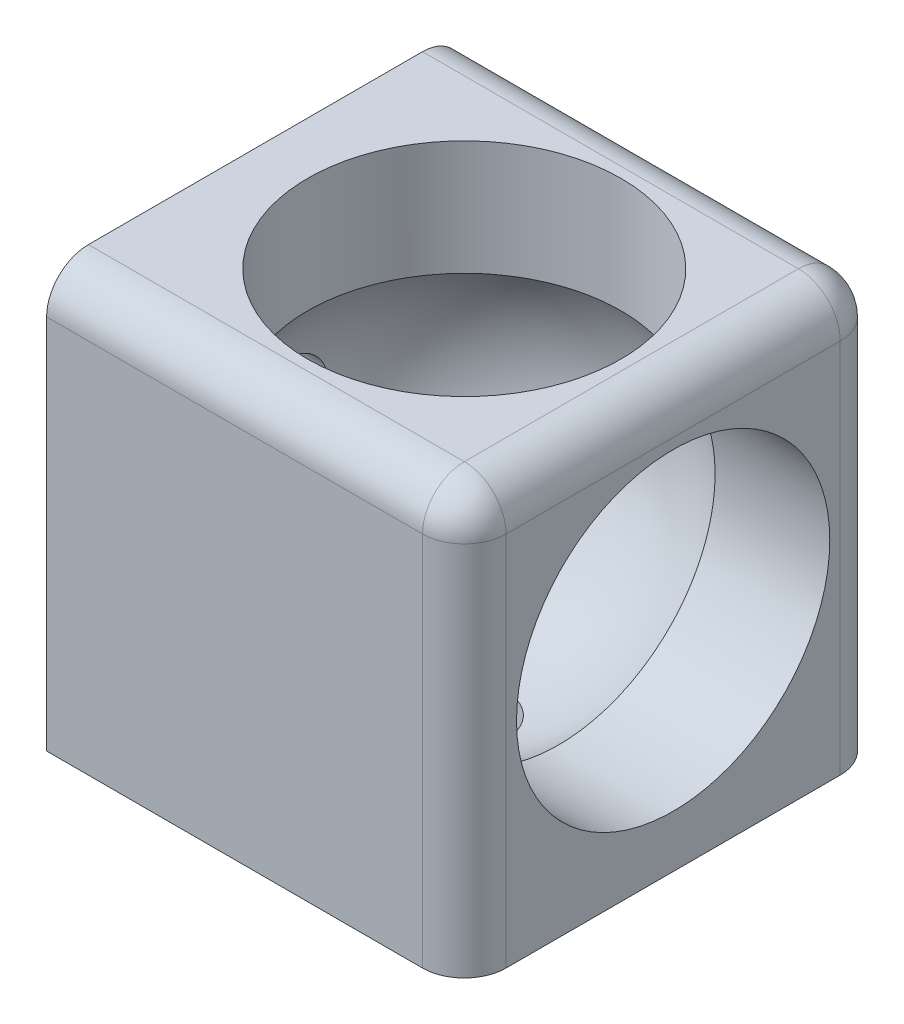
SolidWorks part; units mm, degrees
ref_plane "Ebene vorne" through (0, 0, 0) normal (0, 0, 1) x (1, 0, 0)
ref_plane "Ebene oben" through (0, 0, 0) normal (0, 1, 0) x (1, 0, 0)
ref_plane "Ebene rechts" through (0, 0, 0) normal (1, 0, 0) x (0, 0, -1)
sketch "Sketch1" plane through (0, 0, 0) normal (0, 1, 0) x (1, 0, 0)
  line L1 (20, -20) -> (-20, -20)
  line L2 (20, -20) -> (20, 20)
  line L3 (20, 20) -> (-20, 20)
  line L4 (-20, -20) -> (-20, 20)
  line L5 (20, -20) -> (-20, 20) construction
  line L6 (20, 20) -> (-20, -20) construction
  point P0 (0, 0)
  dimension "D1" = 40
  dimension "D2" = 40
extrude "Boss-Extrude1" add sketch "Sketch1" along normal mid plane 40
fillet "Fillet1" radius 4 5 edges at (0, 20, 20) (20, 0, 20) (20, 20, 0) (20, 0, -20) (0, 20, -20)
sketch "Sketch2" plane through (0, 0, 0) normal (0, 1, 0) x (1, 0, 0)
  line L0 (0, 20.9894) -> (0, -21.3876) construction
  line L1 (0, 17.5) -> (0, -17.5)
  arc A1 (0, 17.5) -> (0, -17.5) centre (0, 0) ccw
  dimension "D1" = 17.5
revolve "Cut-Revolve1" cut sketch "Sketch2" angle 360 about L0
sketch "Sketch12" plane through (0, 20, 0) normal (0, 1, 0) x (1, 0, 0)
  circle A0 centre (0, 0) radius 15
  dimension "D1" = 30
extrude "Cut-Extrude2" cut sketch "Sketch12" against normal blind 20
sketch "Sketch13" plane through (20, 0, 0) normal (1, 0, 0) x (0, 0, -1)
  circle A0 centre (0, 0) radius 15
  dimension "D1" = 30
extrude "Cut-Extrude3" cut sketch "Sketch13" against normal blind 20
sketch "Sketch16" plane through (0, -20, 0) normal (0, -1, 0) x (1, 0, 0)
  circle A0 centre (0, 0) radius 4
  dimension "D1" = 8
extrude "Cut-Extrude6" cut sketch "Sketch16" against normal blind 20
sketch "Sketch17" plane through (-20, 0, 0) normal (-1, 0, 0) x (0, 0, 1)
  circle A0 centre (0, 0) radius 4
  dimension "D1" = 8
extrude "Cut-Extrude7" cut sketch "Sketch17" against normal blind 20
